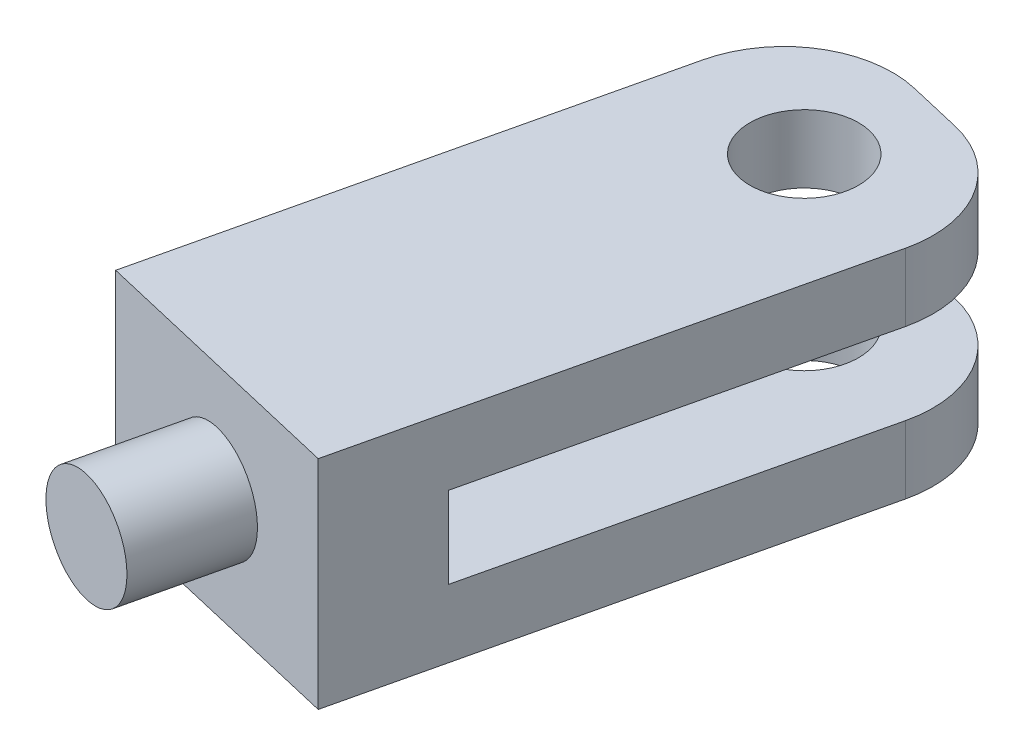
SolidWorks part; units mm, degrees
ref_plane "Front Plane" through (0, 0, 0) normal (0, 0, 1) x (1, 0, 0)
ref_plane "Top Plane" through (0, 0, 0) normal (0, 1, 0) x (1, 0, 0)
ref_plane "Right Plane" through (0, 0, 0) normal (1, 0, 0) x (0, 0, -1)
sketch "Sketch9" plane through (-33.2802, 0, 144.4288) normal (0, 1, 0) x (-0.9737, 0, -0.2278)
  line L0 (0.5028, -148.2127) -> (50.5028, -148.2127)
  line L1 (50.5028, -148.2127) -> (50.5028, -38.2127)
  line L2 (50.5028, -38.2127) -> (0.5028, -38.2127)
  line L3 (0.5028, -38.2127) -> (0.5028, -148.2127)
  dimension "D1" = 50
  dimension "D2" = 110
extrude "Boss-Extrude3" add sketch "Sketch9" against normal blind 40 separate body
sketch "Sketch14" plane through (1.579, -248.4157, 0.3695) normal (-0.2278, 0, 0.9737) x (0.9495, -0.2216, 0.2222)
  line L0 (-102.6072, 218.6156) -> (-99.2838, 203.9884)
  line L1 (-99.2838, 203.9884) -> (-50.5265, 215.0662)
  line L2 (-50.5265, 215.0662) -> (-53.8498, 229.6934)
  line L3 (-53.8498, 229.6934) -> (-102.6072, 218.6156)
  line L7 (-96.5144, 191.7991) -> (-105.3766, 230.805) construction
  line L8 (-96.5144, 191.7991) -> (-105.3766, 230.805) construction
  line L9 (-105.3766, 230.805) -> (-56.6192, 241.8828) construction
  point P4 (-100.9455, 211.302)
  dimension "D1" = 15
  dimension "D2" = 50
extrude "Cut-Extrude4" cut sketch "Sketch14" along normal blind 90
fillet "Fillet2" radius 20 4 edges at (-48.6849, -6.25, -11.3923) (-48.6849, -33.75, -11.3923) (0, -6.25, 0) (0, -33.75, 0)
sketch "Sketch15" plane through (0, -40, 0) normal (0, -1, 0) x (0.9737, 0, 0.2278)
  line L0 (-20, 0) -> (-30, 0) construction
  circle A0 centre (-25, 20) radius 10
  point P2 (-30, 20)
  point P3 (-25, 0)
  dimension "D1" = 20
extrude "Cut-Extrude5" cut sketch "Sketch15" against normal through all
sketch "Sketch22" plane through (-24.8561, -32.5747, 107.1551) normal (-0.2278, 0, 0.9737) x (-0.9466, -0.2343, -0.2215)
  line L0 (50.5548, -4.5445) -> (-7.4245, -31.7181) construction
  circle A0 centre (21.5652, -18.1313) radius 10
  dimension "D1" = 20
extrude "Boss-Extrude4" add sketch "Sketch22" along normal blind 20
